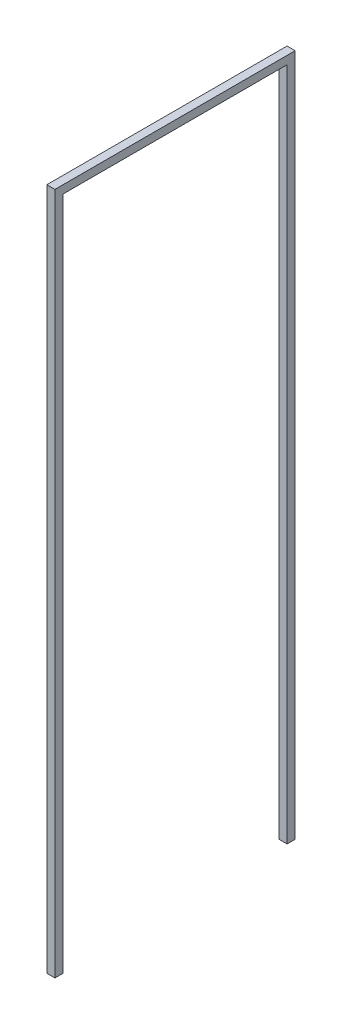
SolidWorks part; units mm, degrees
ref_plane "Front Plane" through (0, 0, 0) normal (0, 0, 1) x (1, 0, 0)
ref_plane "Top Plane" through (0, 0, 0) normal (0, 1, 0) x (1, 0, 0)
ref_plane "Right Plane" through (0, 0, 0) normal (1, 0, 0) x (0, 0, -1)
sketch "Sketch2" plane through (0, 0, 0) normal (1, 0, 0) x (0, 0, -1)
  line L0 (0, 0) -> (0, 2530)
  line L1 (0, 2530) -> (890, 2530)
  line L2 (890, 2530) -> (890, 0)
  line L3 (890, 0) -> (860, 0)
  line L4 (860, 0) -> (860, 2500)
  line L5 (860, 2500) -> (30, 2500)
  line L6 (30, 2500) -> (30, 0)
  line L7 (30, 0) -> (0, 0)
  line L8 (30, 2500) -> (30, 2530)
  line L9 (860, 2500) -> (860, 2530)
  dimension "D1" = 30
  dimension "D2" = 30
  dimension "D3" = 830
  dimension "D4" = 2500
  dimension "D5" = 2500
  dimension "D6" = 30
extrude "Boss-Extrude1" add sketch "Sketch2" along normal mid plane 30 contours L5 L6 L7 L0 L1 L2 L3 L4
sketch "Sketch5" plane through (0, 0, 0) normal (0, -1, 0) x (1, 0, 0)
  line L0 (-15, -890) -> (-15, -860) construction
  line L2 (-15, -30) -> (-15, 0) construction
  line L3 (15, -30) -> (-15, -30) construction
  line L4 (15, -860) -> (-15, -860) construction
  circle A0 centre (0, -15) radius 2.5
  circle A1 centre (0, -875) radius 2.5
  dimension "D2" = 5
  dimension "D3" = 5
  dimension "D1" = 860
  dimension "D4" = 15
  dimension "D5" = 15
  dimension "D6" = 15
  dimension "D7" = 15
extrude "Boss-Extrude3" add sketch "Sketch5" along normal mid plane 5
